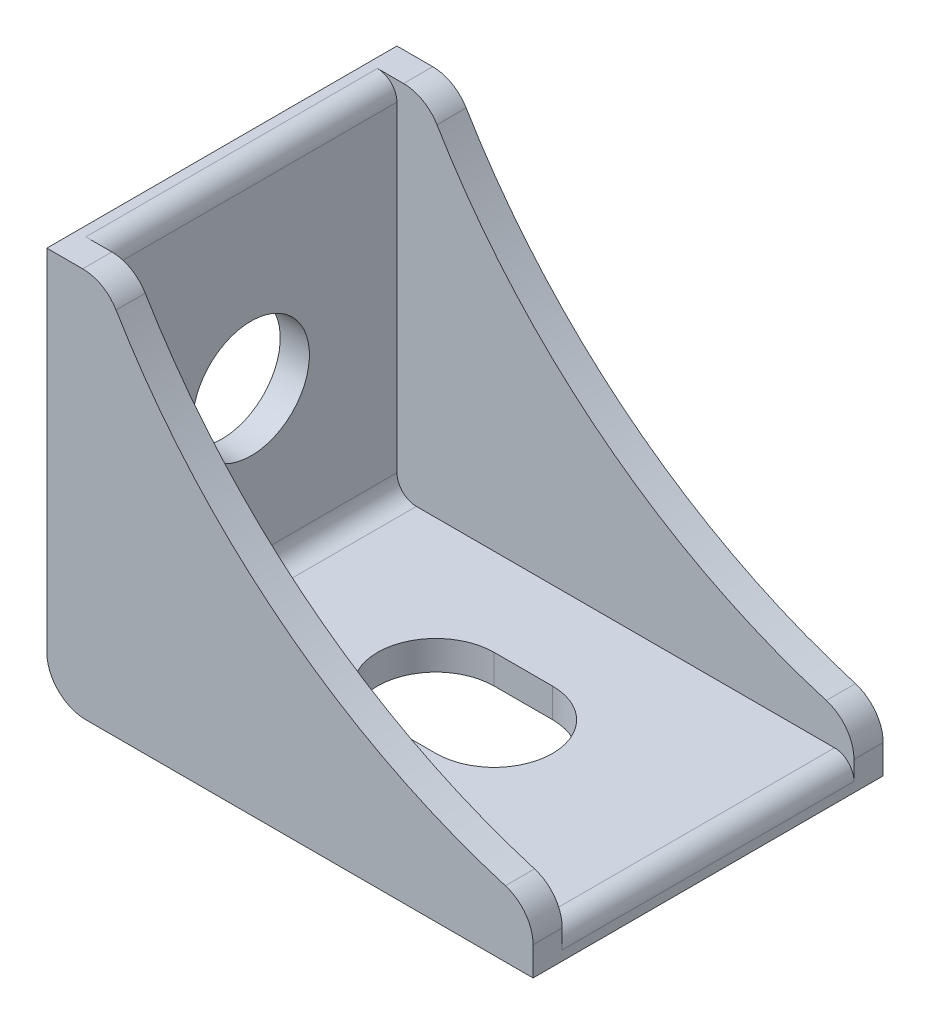
SolidWorks part; units mm, degrees
material "1060 합금"
ref_plane "정면" through (0, 0, 0) normal (0, 0, 1) x (1, 0, 0)
ref_plane "윗면" through (0, 0, 0) normal (0, 1, 0) x (1, 0, 0)
ref_plane "우측면" through (0, 0, 0) normal (1, 0, 0) x (0, 0, -1)
sketch "스케치1" plane through (0, 0, 0) normal (0, 1, 0) x (1, 0, 0)
  line L1 (0, 0) -> (25, 0)
  line L2 (0, 0) -> (0, 18)
  line L3 (0, 18) -> (25, 18)
  line L4 (25, 0) -> (25, 18)
  dimension "D1" = 25
  dimension "D2" = 18
extrude "보스-돌출1" add sketch "스케치1" along normal blind 20
sketch "스케치2" plane through (0, 0, 0) normal (0, 0, 1) x (1, 0, 0)
  line L4 (0, 0) -> (25, 0)
  line L5 (25, 0) -> (25, 20)
  line L6 (25, 20) -> (0, 20)
  line L7 (0, 20) -> (0, 0)
  line L8 (0, 0) -> (25, 0)
  line L9 (25, 0) -> (25, 20)
  line L10 (25, 20) -> (0, 20)
  line L11 (0, 20) -> (0, 0)
  circle A0 centre (33.6402, 36.9168) radius 35
  point P2 (25, 3)
  point P6 (3, 20)
  line M4 (25, 20) -> (0, 20)
  dimension "D1" = 70
  dimension "D3" = 3
  dimension "D4" = 3
  dimension "D2" = 0
extrude "컷-돌출1" cut sketch "스케치2" against normal blind 20 contours A0 L9 M4
sketch "스케치3" plane through (0, 0, 0) normal (-1, 0, 0) x (0, 0, 1)
  line L0 (-18, 20) -> (-18, 0) construction
  line L1 (-18, 20) -> (0, 20) construction
  circle A0 centre (-9, 10) radius 3
  point P6 (-9.1867, 11.4963)
  dimension "D3" = 6
  dimension "D1" = 9
  dimension "D2" = 10
extrude "컷-돌출2" cut sketch "스케치3" against normal through all
sketch "스케치4" plane through (0, 0, 0) normal (0, -1, 0) x (1, 0, 0)
  line L0 (11, -9) -> (14, -9) construction
  line L1 (11, -6) -> (14, -6)
  line L2 (11, -12) -> (14, -12)
  line L4 (25, -18) -> (0, -18) construction
  line L5 (0, -18) -> (0, 0) construction
  arc A0 (11, -6) -> (11, -12) centre (11, -9) ccw
  arc A1 (14, -12) -> (14, -6) centre (14, -9) ccw
  point P2 (12.5, -9)
  point P11 (0, 0)
  point P12 (8, -9)
  point P13 (17, -9)
  dimension "D1" = 3
  dimension "D2" = 9
  dimension "D3" = 9
  dimension "D4" = 12.5
extrude "컷-돌출3" cut sketch "스케치4" against normal through all
sketch "스케치5" plane through (0, 20, 0) normal (0, 1, 0) x (1, 0, 0)
  line L0 (0, 18) -> (0, 0) construction
  line L1 (1.5, 1.5) -> (25, 1.5)
  line L2 (1.5, 1.5) -> (1.5, 16.5)
  line L3 (1.5, 16.5) -> (25, 16.5)
  line L4 (25, 1.5) -> (25, 16.5)
  line L5 (0, 0) -> (3, 0) construction
  line L6 (3, 18) -> (0, 18) construction
  line L7 (25, 18) -> (25, 0) construction
  dimension "D1" = 1.5
  dimension "D2" = 1.5
  dimension "D3" = 1.5
extrude "컷-돌출4" cut sketch "스케치5" against normal blind 18.5
fillet "필렛1" radius 1 3 edges at (25, 1.5, -9) (1.5, 1.5, -9) (1.5, 20, -9)
fillet "필렛2" radius 2 5 edges at (0, 0, -9) (3, 20, -17.25) (25, 3, -17.25) (25, 3, -0.75) (3, 20, -0.75)
